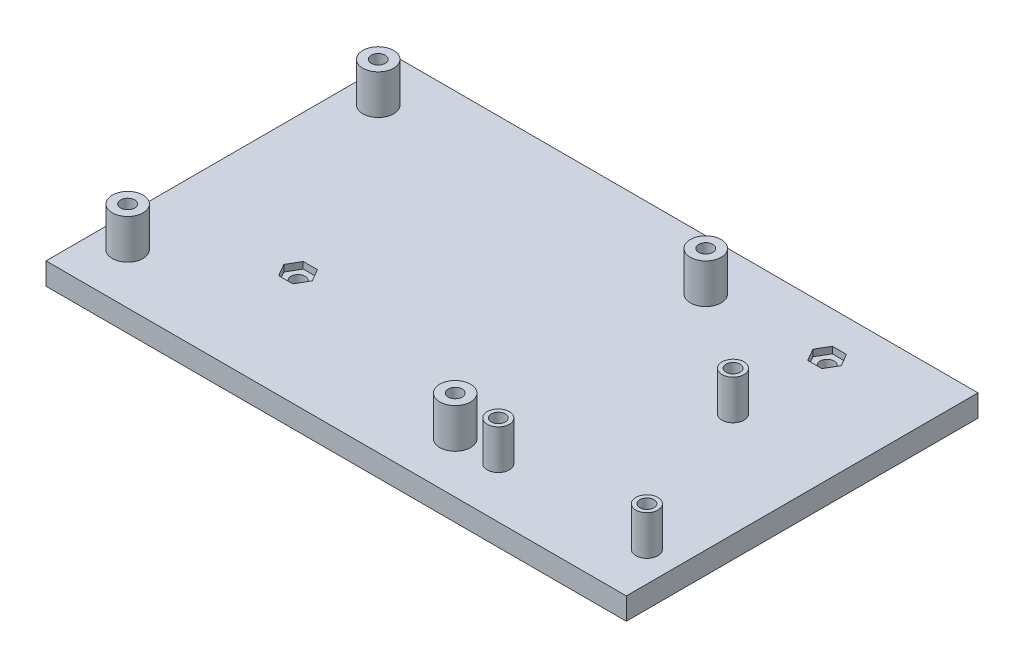
SolidWorks part; units mm, degrees
ref_plane "Front Plane" through (0, 0, 0) normal (0, 0, 1) x (1, 0, 0)
ref_plane "Top Plane" through (0, 0, 0) normal (0, 1, 0) x (1, 0, 0)
ref_plane "Right Plane" through (0, 0, 0) normal (1, 0, 0) x (0, 0, -1)
sketch "Sketch1" plane through (0, 0, 0) normal (0, 1, 0) x (1, 0, 0)
  line L1 (-66, 40) -> (66, 40)
  line L2 (-66, 40) -> (-66, -40)
  line L3 (-66, -40) -> (66, -40)
  line L4 (66, 40) -> (66, -40)
  line L5 (-66, 40) -> (66, -40) construction
  line L6 (-66, -40) -> (66, 40) construction
  point P0 (0, 0)
  dimension "D1" = 132
  dimension "D2" = 80
extrude "Boss-Extrude1" add sketch "Sketch1" along normal blind 5
sketch "Sketch2" plane through (0, 5, 0) normal (0, 1, 0) x (1, 0, 0)
  line L0 (-66, 40) -> (-66, -40) construction
  line L1 (-58.9215, 28.5) -> (15.5785, 28.5) construction
  line L2 (-58.9215, 28.5) -> (-58.9215, -28.5) construction
  line L3 (-58.9215, -28.5) -> (15.5785, -28.5) construction
  line L4 (15.5785, 28.5) -> (15.5785, -28.5) construction
  line L5 (-66, 0) -> (66, 0) construction
  line L6 (66, -40) -> (66, 40) construction
  line L7 (42.2787, -28.5) -> (42.2787, 8) construction
  line L8 (25.3787, -28.5) -> (59.1787, -28.5) construction
  line L9 (25.3787, -28.5) -> (25.3787, 8) construction
  line L10 (25.3787, 8) -> (59.1787, 8) construction
  line L11 (59.1787, -28.5) -> (59.1787, 8) construction
  circle A0 centre (42.2787, 8) radius 1.6
  circle A1 centre (25.3787, -28.5) radius 1.6
  circle A2 centre (59.1787, -28.5) radius 1.6
  circle A3 centre (15.5785, 28.5) radius 1.6
  circle A4 centre (15.5785, -28.5) radius 1.6
  circle A5 centre (-58.9215, -28.5) radius 1.6
  circle A6 centre (-58.9215, 28.5) radius 1.6
  point P10 (-58.9215, 0)
  point P24 (0, 0)
  dimension "D6" = 3.2
  dimension "D1" = 74.5
  dimension "D2" = 57
  dimension "D3" = 7.0785
  dimension "D4" = 33.8
  dimension "D5" = 36.5
sketch "Sketch3" plane through (0, 5, 0) normal (0, 1, 0) x (1, 0, 0)
  circle A0 centre (-58.9215, 28.5) radius 3.5
  circle A1 centre (15.5785, 28.5) radius 3.5
  circle A2 centre (15.5785, -28.5) radius 3.5
  circle A3 centre (-58.9215, -28.5) radius 3.5
  circle A4 centre (25.3787, -28.5) radius 2.5
  circle A5 centre (59.1787, -28.5) radius 2.5
  circle A6 centre (42.2787, 8) radius 2.5
  dimension "D1" = 5
  dimension "D2" = 7
extrude "Boss-Extrude2" add sketch "Sketch3" along normal blind 9
extrude "Cut-Extrude1" cut sketch "Sketch2" against normal up to next and the other way up to next
sketch "Sketch4" plane through (0, 0, 0) normal (0, -1, 0) x (1, 0, 0)
  circle A0 centre (42.2787, -8) radius 3.05
  circle A1 centre (59.1787, 28.5) radius 3.05
  circle A2 centre (25.3787, 28.5) radius 3.05
  circle A3 centre (15.5785, 28.5) radius 3.05
  circle A4 centre (15.5785, -28.5) radius 3.05
  circle A5 centre (-58.9215, -28.5) radius 3.05
  circle A6 centre (-58.9215, 28.5) radius 3.05
  dimension "D1" = 6.1
extrude "Cut-Extrude2" cut sketch "Sketch4" against normal blind 3.2
sketch "Sketch5" plane through (0, 5, 0) normal (0, 1, 0) x (1, 0, 0)
  circle A0 centre (-35.0119, -13.6573) radius 1.6
  circle A1 centre (41.8615, 29.8149) radius 1.6
  dimension "D1" = 3.2
  dimension "D2" = 3.2
extrude "Cut-Extrude3" cut sketch "Sketch5" against normal up to next
sketch "Sketch6" plane through (0, 5, 0) normal (0, 1, 0) x (1, 0, 0)
  line L0 (66, 40) -> (-66, 40) construction
  line L1 (-33.3953, -16.4573) -> (-31.7787, -13.6573)
  line L2 (-31.7787, -13.6573) -> (-33.3953, -10.8573)
  line L3 (-33.3953, -10.8573) -> (-36.6284, -10.8573)
  line L4 (-36.6284, -10.8573) -> (-38.245, -13.6573)
  line L5 (-38.245, -13.6573) -> (-36.6284, -16.4573)
  line L6 (-36.6284, -16.4573) -> (-33.3953, -16.4573)
  line L7 (43.4781, 27.0149) -> (45.0946, 29.8149)
  line L8 (45.0946, 29.8149) -> (43.4781, 32.6149)
  line L9 (43.4781, 32.6149) -> (40.2449, 32.6149)
  line L10 (40.2449, 32.6149) -> (38.6283, 29.8149)
  line L11 (38.6283, 29.8149) -> (40.2449, 27.0149)
  line L12 (40.2449, 27.0149) -> (43.4781, 27.0149)
  circle A0 centre (-35.0119, -13.6573) radius 2.8 construction
  circle A1 centre (41.8615, 29.8149) radius 2.8 construction
  dimension "D1" = 5.6
  dimension "D2" = 5.6
extrude "Cut-Extrude4" cut sketch "Sketch6" against normal blind 1.5
